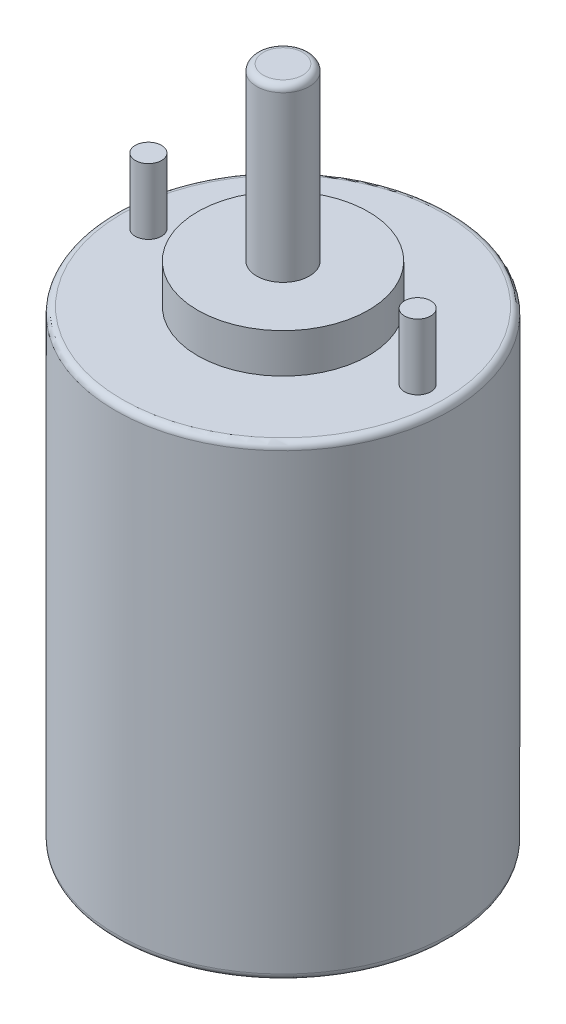
SolidWorks part; units mm, degrees
ref_plane "Front Plane" through (0, 0, 0) normal (0, 0, 1) x (1, 0, 0)
ref_plane "Top Plane" through (0, 0, 0) normal (0, 1, 0) x (1, 0, 0)
ref_plane "Right Plane" through (0, 0, 0) normal (1, 0, 0) x (0, 0, -1)
sketch "Sketch2" plane through (0, 0, 0) normal (0, 1, 0) x (1, 0, 0)
  circle A0 centre (0, 0) radius 25.5
  dimension "D1" = 51
extrude "Boss-Extrude1" add sketch "Sketch2" along normal mid plane 65
sketch "Sketch3" plane through (0, 32.5, 0) normal (0, 1, 0) x (1, 0, 0)
  circle A0 centre (0, 0) radius 25.5
extrude "Boss-Extrude2" add sketch "Sketch3" along normal blind 3
fillet "Fillet1" radius 1 1 edges at (0, 35.5, 25.5)
sketch "Sketch4" plane through (0, 35.5, 0) normal (0, 1, 0) x (1, 0, 0)
  circle A0 centre (0, 0) radius 13
  dimension "D1" = 26
extrude "Boss-Extrude3" add sketch "Sketch4" along normal blind 6
mirror "Mirror1" about plane through (0, 0, 0) normal (0, 1, 0) of "Boss-Extrude3", "Fillet1", "Boss-Extrude2"
sketch "Sketch5" plane through (0, 41.5, 0) normal (0, 1, 0) x (1, 0, 0)
  circle A0 centre (0, 0) radius 4
  dimension "D1" = 8
extrude "Boss-Extrude4" add sketch "Sketch5" along normal blind 26
sketch "Sketch6" plane through (0, 35.5, 0) normal (0, 1, 0) x (1, 0, 0)
  circle A0 centre (0, 0) radius 20.5 construction
  circle A1 centre (-20.5, 0) radius 2
  circle A2 centre (20.5, 0) radius 2
  dimension "D1" = 4
  dimension "D2" = 41
extrude "Boss-Extrude5" add sketch "Sketch6" along normal blind 10
fillet "Fillet2" radius 1 1 edges at (0, 67.5, 4)
